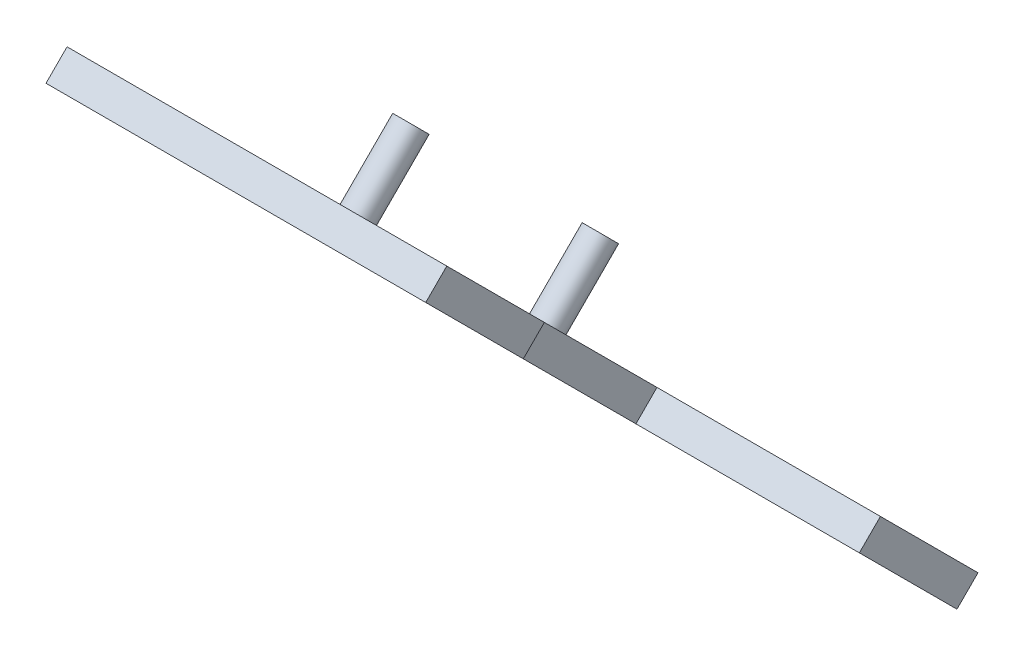
SolidWorks part; units mm, degrees
ref_plane "Plano frontal" through (0, 0, 0) normal (0, 0, 1) x (1, 0, 0)
ref_plane "Plano superior" through (0, 0, 0) normal (0, 1, 0) x (1, 0, 0)
ref_plane "Plano direito" through (0, 0, 0) normal (1, 0, 0) x (0, 0, -1)
sketch "Sketch2" plane through (0, 0, 0) normal (1, 0, 0) x (0, 0, -1)
  line L0 (-40415.6746, 2982.7521) -> (-40415.6746, 3011.0364)
  line L1 (-40415.6746, 3011.0364) -> (-40072.9302, 2668.2921)
  line L2 (-40072.9302, 2668.2921) -> (-40072.9302, 2640.0078)
  line L3 (-40072.9302, 2640.0078) -> (-40415.6746, 2982.7521)
  line L4 (-40415.6746, 2982.7521) -> (-40429.8167, 2996.8942)
  line L5 (-40329.4082, 2896.4858) -> (-40559.1473, 3126.2249) construction
  line L6 (-40429.8167, 2996.8942) -> (-40415.6746, 3011.0364)
  line L7 (-40072.9302, 2668.2921) -> (-40058.7881, 2654.1499)
  line L8 (-40058.7881, 2654.1499) -> (-40072.9302, 2640.0078)
  dimension "D1" = 45
  dimension "D2" = 20
extrude "Boss-Extrude1" add sketch "Sketch2" against normal blind 100 and the other way blind 5 from offset 23110 contours L6 L4 L0 | L3 L2 L1 L0 | L8 L7 L2 offset against normal yes
sketch "Sketch3" plane through (0, -18716.4612, 18716.4612) normal (0, -0.7071, 0.7071) x (1, 0, 0)
  line L0 (-23105, 30614.6071) -> (-23105, 30295.3228) construction
  line L1 (-23105, 30707.3218) -> (-22954.8819, 30707.3218)
  line L2 (-23105, 30707.3218) -> (-23105, 30614.6071)
  line L3 (-23105, 30614.6071) -> (-22954.8819, 30614.6071)
  line L4 (-22954.8819, 30707.3218) -> (-22954.8819, 30614.6071)
  line L5 (-23105, 30295.3228) -> (-22954.8819, 30295.3228)
  line L6 (-23105, 30295.3228) -> (-23105, 30202.6081)
  line L7 (-23105, 30202.6081) -> (-22954.8819, 30202.6081)
  line L8 (-22954.8819, 30295.3228) -> (-22954.8819, 30202.6081)
  line L9 (-23105, 30707.3218) -> (-23210, 30707.3218) construction
  line L10 (-23105, 30202.6081) -> (-23210, 30202.6081) construction
extrude "Boss-Extrude2" add sketch "Sketch3" against normal blind 20
sketch "Sketch4" plane through (0, -18702.3191, 18702.3191) normal (0, 0.7071, -0.7071) x (1, 0, 0)
  circle A0 centre (-23146.2304, -30340.7947) radius 10
  circle A2 centre (-23146.2304, -30520.7947) radius 10
  dimension "D1" = 20
  dimension "D2" = 2
extrude "Boss-Extrude3" add sketch "Sketch4" along normal blind 50
ref_plane "Plane1" through (0, -18688.1769, 18688.1769) normal (0, 0.7071, -0.7071) x (-1, 0, 0)
sketch "Sketch6" plane through (0, -18688.1769, 18688.1769) normal (0, 0.7071, -0.7071) x (-1, 0, 0)
  point P0 (23146.2304, 30340.7947)
